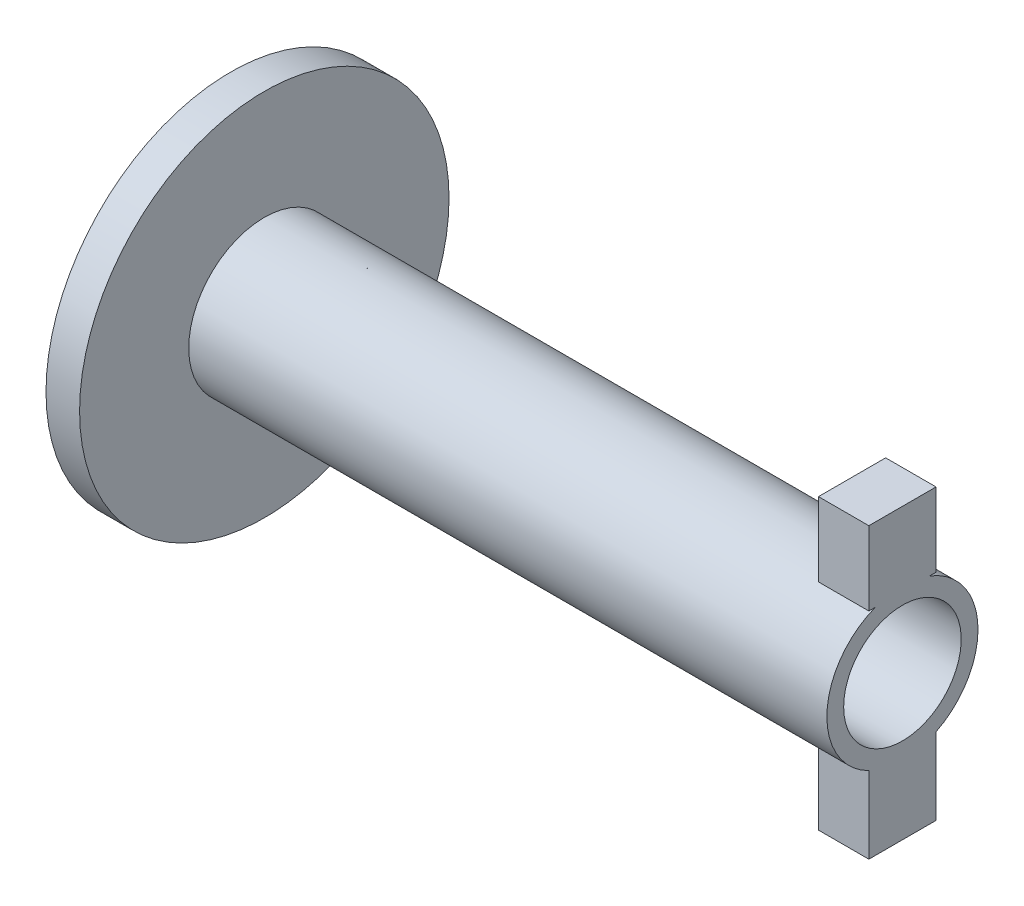
SolidWorks part; units mm, degrees
ref_plane "Front Plane" through (0, 0, 0) normal (0, 0, 1) x (1, 0, 0)
ref_plane "Top Plane" through (0, 0, 0) normal (0, 1, 0) x (1, 0, 0)
ref_plane "Right Plane" through (0, 0, 0) normal (1, 0, 0) x (0, 0, -1)
sketch "Sketch2" plane through (0, 0, 0) normal (1, 0, 0) x (0, 0, -1)
  circle A0 centre (0, 0) radius 55
extrude "Boss-Extrude1" add sketch "Sketch2" along normal blind 10
sketch "Sketch3" plane through (10, 0, 0) normal (1, 0, 0) x (0, 0, -1)
  circle A0 centre (0, 0) radius 22.5
extrude "Boss-Extrude2" add sketch "Sketch3" along normal blind 190
sketch "Sketch4" plane through (0, 0, 0) normal (-1, 0, 0) x (0, 0, 1)
  circle A0 centre (0, 0) radius 17.5
extrude "Cut-Extrude1" cut sketch "Sketch4" against normal through all both and the other way through all
sketch "Sketch9" plane through (200, 0, 0) normal (1, 0, 0) x (0, 0, -1)
  line L1 (-10, 43) -> (10, 43)
  line L2 (-10, 43) -> (-10, 21)
  line L3 (-10, 21) -> (10, 21)
  line L4 (10, 43) -> (10, 21)
  line L5 (-10, 43) -> (10, 21) construction
  line L6 (-10, 21) -> (10, 43) construction
  point P0 (0, 32)
extrude "Boss-Extrude3" add sketch "Sketch9" against normal blind 15
sketch "Sketch10" plane through (200, 0, 0) normal (1, 0, 0) x (0, 0, -1)
  line L1 (-10, -20) -> (10, -20)
  line L2 (-10, -20) -> (-10, -43)
  line L3 (-10, -43) -> (10, -43)
  line L4 (10, -20) -> (10, -43)
  line L5 (-10, -20) -> (10, -43) construction
  line L6 (-10, -43) -> (10, -20) construction
  point P0 (0, -31.5)
extrude "Boss-Extrude4" add sketch "Sketch10" against normal blind 15
